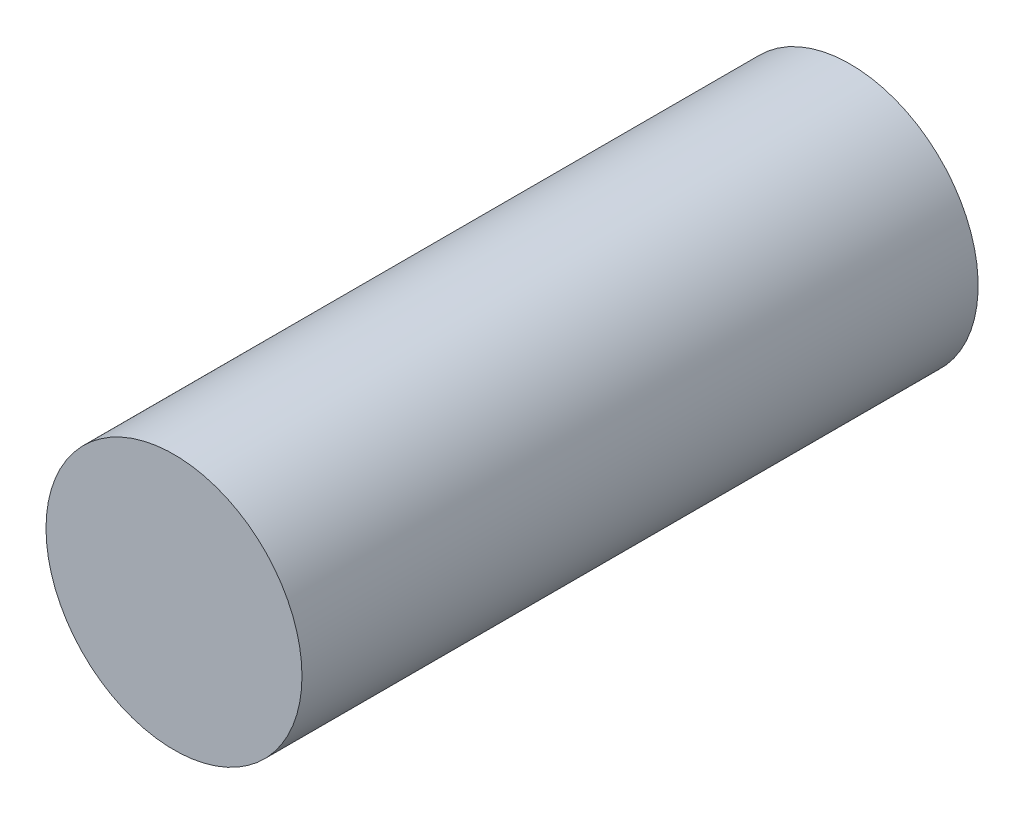
SolidWorks part; units mm, degrees
ref_plane "Front Plane" through (0, 0, 0) normal (0, 0, 1) x (1, 0, 0)
ref_plane "Top Plane" through (0, 0, 0) normal (0, 1, 0) x (1, 0, 0)
ref_plane "Right Plane" through (0, 0, 0) normal (1, 0, 0) x (0, 0, -1)
sketch "Sketch1" plane through (0, 0, 0) normal (0, 0, 1) x (1, 0, 0)
  circle A0 centre (0, 0) radius 50.8
  dimension "D1" = 101.6
extrude "Boss-Extrude1" add sketch "Sketch1" along normal blind 304.8
sketch "Sketch2" plane through (0, 0, 0) normal (0, 0, -1) x (-1, 0, 0)
  line L0 (0, -62.5) -> (0, 62.5) construction
  line L1 (0, 62.5) -> (0, -62.5)
  arc A0 (0, -62.5) -> (0, 62.5) centre (0, 0) ccw
  dimension "D1" = 125
revolve "Cut-Revolve3" cut sketch "Sketch2" angle 180 about L0
sketch "Sketch4" plane through (0, 0, 0) normal (1, 0, 0) x (0, 0, -1)
  line L0 (-36.4089, 50.8) -> (-304.8, 50.8) construction
